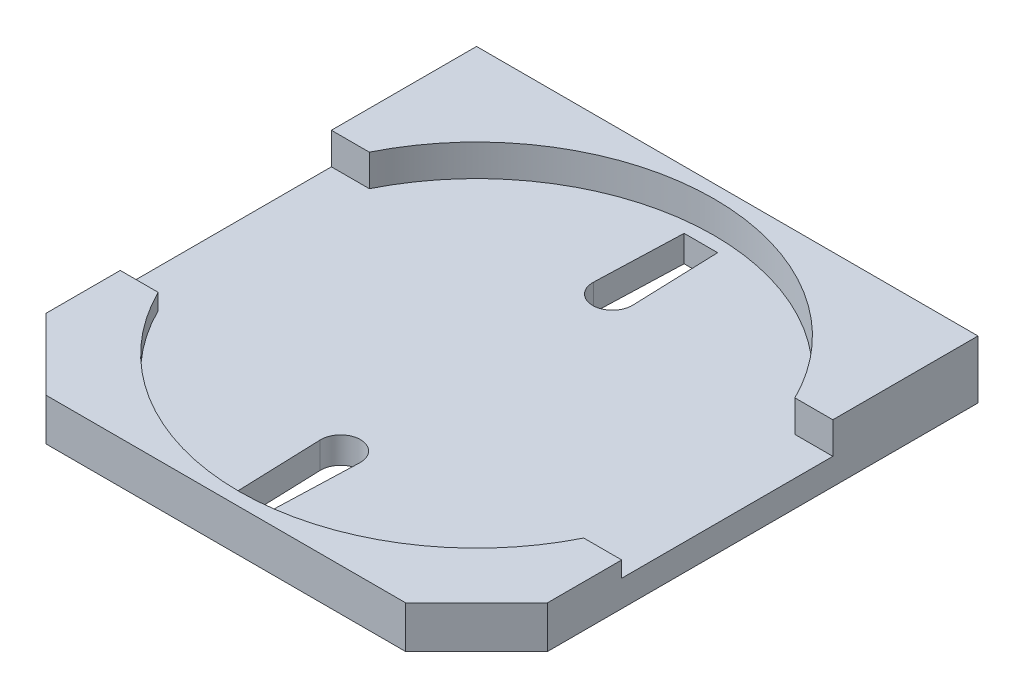
SolidWorks part; units mm, degrees
ref_plane "Front Plane" through (0, 0, 0) normal (0, 0, 1) x (1, 0, 0)
ref_plane "Top Plane" through (0, 0, 0) normal (0, 1, 0) x (1, 0, 0)
ref_plane "Right Plane" through (0, 0, 0) normal (1, 0, 0) x (0, 0, -1)
sketch "Sketch1" plane through (0, 0, 0) normal (0, 1, 0) x (1, 0, 0)
  line L1 (-9.5, -9.5) -> (9.5, -9.5)
  line L2 (-9.5, -9.5) -> (-9.5, 9.5)
  line L3 (-9.5, 9.5) -> (9.5, 9.5)
  line L4 (9.5, -9.5) -> (9.5, 9.5)
  line L5 (-9.5, -9.5) -> (9.5, 9.5) construction
  line L6 (-9.5, 9.5) -> (9.5, -9.5) construction
  point P0 (0, 0)
  dimension "D1" = 19
extrude "Boss-Extrude1" add sketch "Sketch1" along normal blind 3.5
sketch "Sketch2" plane through (0, 3.5, 0) normal (0, 1, 0) x (1, 0, 0)
  line L0 (-9.5, -6.813) -> (-6.813, -9.5)
  line L1 (-9.5, 9.5) -> (-9.5, -9.5) construction
  line L2 (-9.5, -9.5) -> (9.5, -9.5) construction
  line L3 (-6.813, -9.5) -> (-9.5, -9.5)
  line L4 (-9.5, -9.5) -> (-9.5, -6.813)
  dimension "D1" = 3.8
extrude "Cut-Extrude1" cut sketch "Sketch2" against normal through all
mirror "Mirror1" about plane through (0, 0, 0) normal (1, 0, 0) of "Cut-Extrude1"
sketch "Sketch3" plane through (0, 3.5, 0) normal (0, 1, 0) x (1, 0, 0)
  line L0 (-9.5, 4) -> (9.5, 4)
  line L1 (-9.5, 9.5) -> (-9.5, -6.813) construction
  line L2 (9.5, -6.813) -> (9.5, 9.5) construction
  line L3 (9.5, 4) -> (9.5, -6.813)
  line L4 (9.5, -6.813) -> (6.813, -9.5)
  line L5 (6.813, -9.5) -> (-6.813, -9.5)
  line L6 (-6.813, -9.5) -> (-9.5, -6.813)
  line L7 (-9.5, -6.813) -> (-9.5, 4)
  line L8 (9.5, 9.5) -> (-9.5, 9.5) construction
  dimension "D1" = 5.5
extrude "Cut-Extrude2" cut sketch "Sketch3" against normal blind 0.6
sketch "Sketch5" plane through (0, 2.9, 0) normal (0, 1, 0) x (1, 0, 0)
  line L0 (9.5, -6.813) -> (9.5, 4) construction
  line L1 (-9.5, 4) -> (9.5, 4)
  line L2 (-9.5, 4) -> (-9.5, -4)
  line L3 (-9.5, -4) -> (9.5, -4)
  line L4 (9.5, 4) -> (9.5, -4)
  line L5 (-55, 0) -> (55, 0) construction
  point P7 (-9.5, 0)
extrude "Cut-Extrude3" cut sketch "Sketch5" against normal blind 0.6
sketch "Sketch6" plane through (0, 3.5, 0) normal (0, 1, 0) x (1, 0, 0)
  circle A0 centre (0, 0) radius 9
  dimension "D1" = 18
extrude "Cut-Extrude4" cut sketch "Sketch6" against normal blind 1.2
sketch "Sketch7" plane through (0, 0, 0) normal (0, -1, 0) x (1, 0, 0)
  line L0 (0, -1.925) -> (0, 1.925) construction
  circle A0 centre (-5.5, -6.2009) radius 1.25
  circle A1 centre (-5.5, 5.2991) radius 1.25
  circle A2 centre (5.5, 5.2991) radius 1.25
  circle A3 centre (5.5, -6.2009) radius 1.25
  dimension "D1" = 2.5
  dimension "D2" = 5.5
  dimension "D3" = 11.5
extrude "Cut-Extrude5" cut sketch "Sketch7" against normal blind 1.3 flip side to cut
sketch "Sketch8" plane through (0, 1.3, 0) normal (0, -1, 0) x (1, 0, 0)
  line L0 (-0.6, -9.5) -> (0.6, -9.5)
  line L1 (-9.5, -9.5) -> (9.5, -9.5) construction
  line L2 (0, -1.925) -> (0, 1.925) construction
  line L4 (0.6, -9.5) -> (0.7496, -5.1759)
  line L5 (-0.6, -9.5) -> (-0.7496, -5.1759)
  arc A0 (0.7496, -5.1759) -> (-0.7496, -5.1759) centre (0, -5.15) ccw
  point P4 (0, -9.5)
  dimension "D2" = 1.5
  dimension "D1" = 1.2
  dimension "D3" = 4.35
extrude "Cut-Extrude6" cut sketch "Sketch8" against normal blind 1
mirror "Mirror2" about plane through (0, 0, 0) normal (0, 0, 1) of "Cut-Extrude6"
sketch "Sketch11" plane through (0, 1.3, 0) normal (0, -1, 0) x (1, 0, 0)
  line L0 (-0.6, -9.5) -> (0.6, -9.5)
  line L1 (0.6, -9.5) -> (0.6346, -8.5)
  line L2 (0.6, -9.5) -> (0.7496, -5.1759) construction
  line L3 (0.6346, -8.5) -> (-0.6346, -8.5)
  line L4 (-0.7496, -5.1759) -> (-0.6, -9.5) construction
  line L5 (-0.6346, -8.5) -> (-0.6, -9.5)
  dimension "D1" = 1
extrude "Boss-Extrude4" add sketch "Sketch11" against normal blind 1
mirror "Mirror3" about plane through (0, 0, 0) normal (0, 0, 1) of "Boss-Extrude4"
